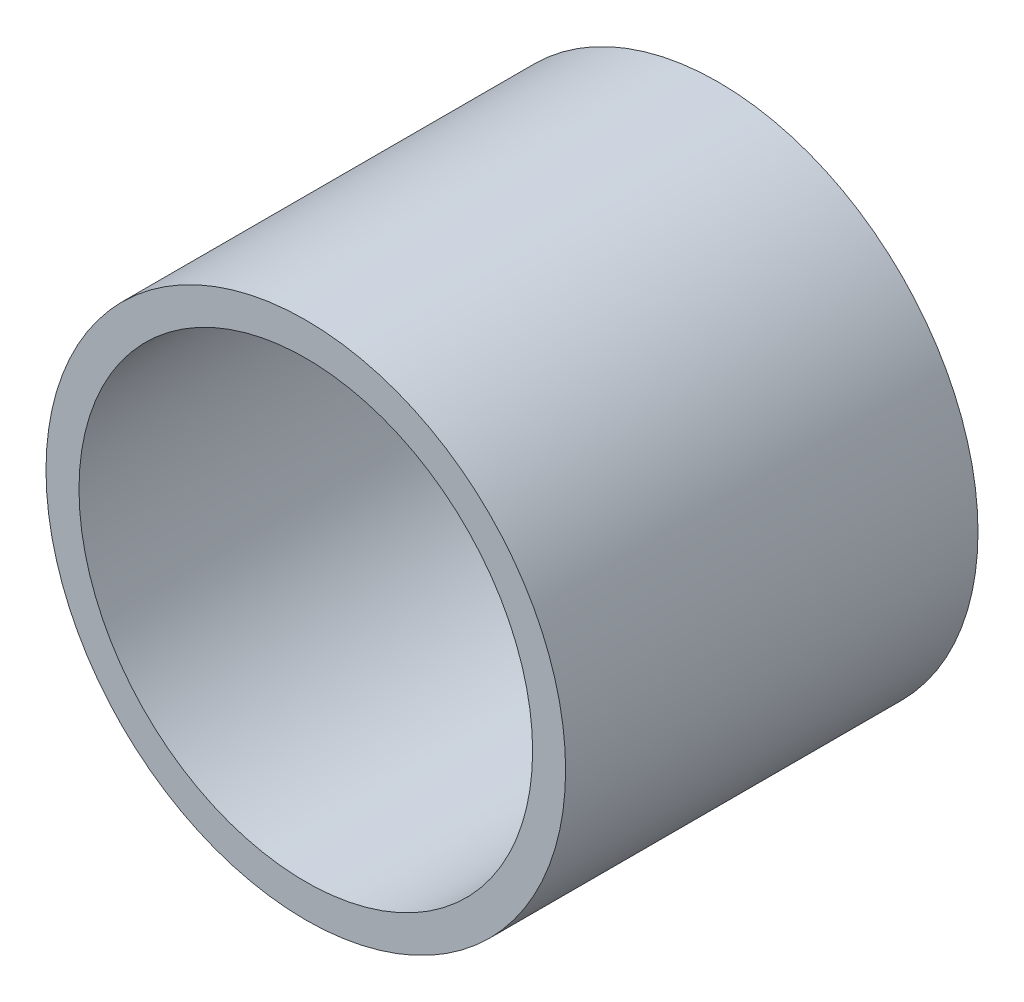
SolidWorks part; units mm, degrees
material "Brass"
ref_plane "Front Plane" through (0, 0, 0) normal (0, 0, 1) x (1, 0, 0)
ref_plane "Top Plane" through (0, 0, 0) normal (0, 1, 0) x (1, 0, 0)
ref_plane "Right Plane" through (0, 0, 0) normal (1, 0, 0) x (0, 0, -1)
sketch "Sketch1" plane through (0, 0, 0) normal (0, 0, 1) x (1, 0, 0)
  circle A0 centre (0, 0) radius 27.5
  circle A1 centre (0, 0) radius 31.5
  dimension "D1" = 55
  dimension "D2" = 4
extrude "Boss-Extrude1" add sketch "Sketch1" along normal blind 50
